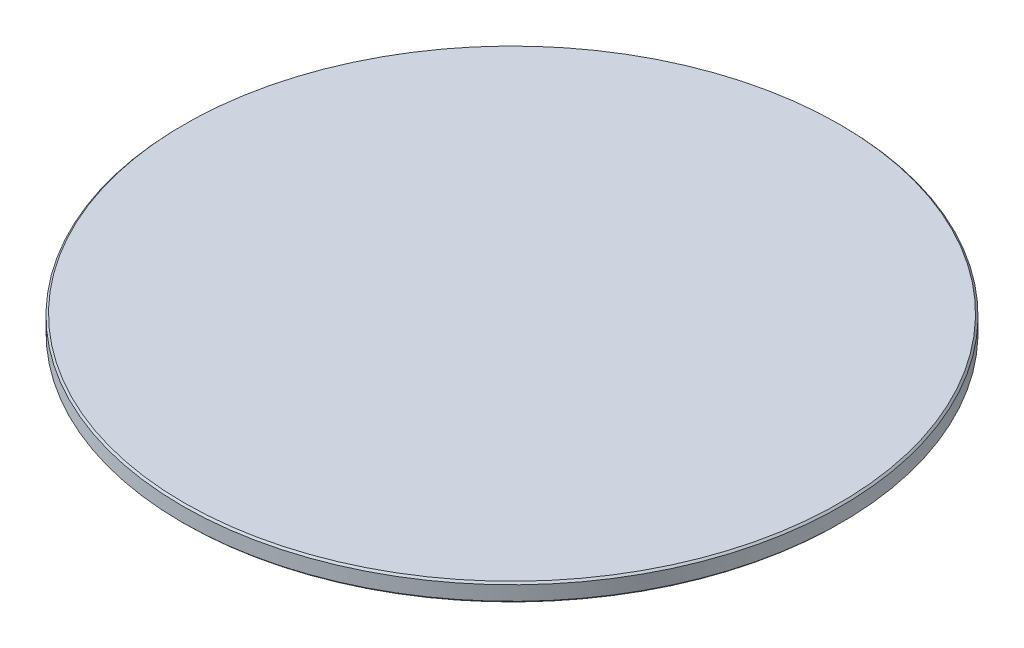
SolidWorks part; units mm, degrees
ref_plane "Front Plane" through (0, 0, 0) normal (0, 0, 1) x (1, 0, 0)
ref_plane "Top Plane" through (0, 0, 0) normal (0, 1, 0) x (1, 0, 0)
ref_plane "Right Plane" through (0, 0, 0) normal (1, 0, 0) x (0, 0, -1)
sketch "Sketch1" plane through (0, 0, 0) normal (0, 0, 1) x (1, 0, 0)
  line L0 (0, 0) -> (92, 0)
  line L1 (92, 0) -> (92, -5)
  line L2 (92, -5) -> (90.1, -5)
  line L3 (90.1, -5) -> (90.1, -2)
  line L4 (90.1, -2) -> (84.9, -2)
  line L5 (84.9, -2) -> (84.9, -5)
  line L6 (84.9, -5) -> (83, -5)
  line L7 (83, -5) -> (83, -1.2)
  line L8 (83, -1.2) -> (0, -1.2)
  line L9 (0, -1.2) -> (0, 0)
  dimension "D1" = 84.9
  dimension "D2" = 5.2
  dimension "D3" = 3
  dimension "D4" = 1.9
  dimension "D5" = 1.9
  dimension "D6" = 1.2
  dimension "D7" = 2
revolve "Revolve1" add sketch "Sketch1" angle 360 about L9
chamfer "Chamfer1" distance 0.5 angle 45 6 edges at (0, 0, -92) (0, -1.2, -83) (0, -5, -83) (0, -5, -84.9) (0, -5, -90.1) (0, -5, -92)
